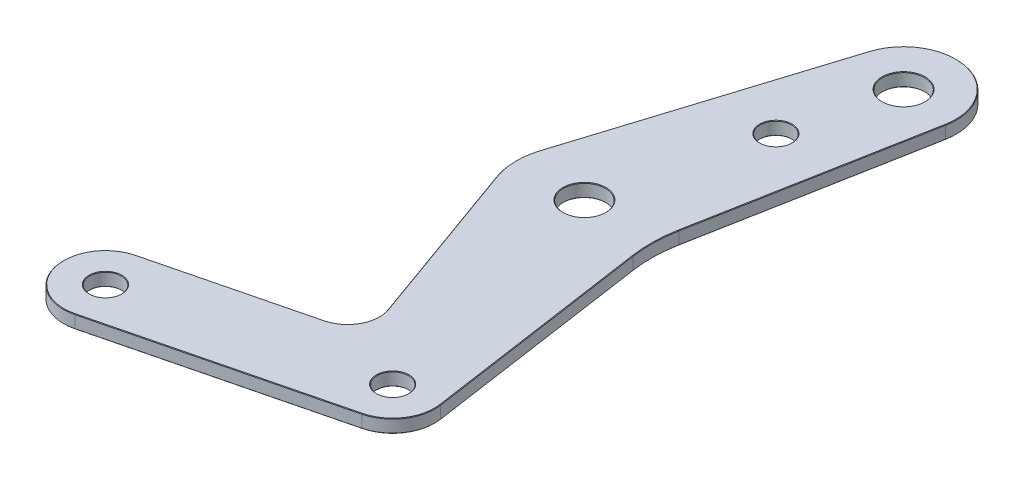
SolidWorks part; units mm, degrees
material "Plain Carbon Steel"
ref_plane "Front Plane" through (0, 0, 0) normal (0, 0, 1) x (1, 0, 0)
ref_plane "Top Plane" through (0, 0, 0) normal (0, 1, 0) x (1, 0, 0)
ref_plane "Right Plane" through (0, 0, 0) normal (1, 0, 0) x (0, 0, -1)
sketch "Sketch1" plane through (0, 0, 0) normal (0, 1, 0) x (1, 0, 0)
  line L0 (0, 0) -> (12.0961, 48.5148) construction
  line L1 (0, 0) -> (0, 50000) construction
  line L2 (0, 0) -> (50000, 0) construction
  line L3 (0, 0) -> (12.0961, -48.5148) construction
  line L4 (12.0961, -48.5148) -> (-31.5672, -59.4013) construction
  line L5 (-29.6318, -67.1636) -> (14.0315, -56.2772)
  line L6 (-33.5026, -51.6389) -> (-4.8571, -44.4968)
  line L7 (2.5558, 51.5118) -> (-12.4024, 3.8961)
  line L8 (-12.2361, -4.3906) -> (-0.6612, -36.6486)
  line L9 (13.7938, -4.5289) -> (20.0131, -47.3653)
  line L10 (21.9267, 46.6821) -> (13.9644, 3.9718)
  circle A0 centre (0, 0) radius 4
  circle A1 centre (12.0961, 48.5148) radius 4
  circle A2 centre (7.2577, 29.1089) radius 3
  circle A3 centre (12.0961, -48.5148) radius 3
  circle A4 centre (-31.5672, -59.4013) radius 3
  arc A5 (-33.5026, -51.6389) -> (-29.6318, -67.1636) centre (-31.5672, -59.4013) ccw
  arc A6 (14.0315, -56.2772) -> (20.0131, -47.3653) centre (12.0961, -48.5148) ccw
  arc A8 (21.9267, 46.6821) -> (2.5558, 51.5118) centre (12.0961, 48.5148) ccw
  arc A9 (-4.8571, -44.4968) -> (-0.6612, -36.6486) centre (-6.3086, -38.675) ccw
  arc A10 (-12.4024, 3.8961) -> (-12.2361, -4.3906) centre (0, 0) ccw
  arc A11 (13.7938, -4.5289) -> (13.9644, 3.9718) centre (39.5241, -0.7932) cw
  dimension "D1" = 8
  dimension "D4" = 8
  dimension "D5" = 6
  dimension "D9" = 6
  dimension "D11" = 6
  dimension "D12" = 16
  dimension "D13" = 16
  dimension "D14" = 26
  dimension "D15" = 20
  dimension "D16" = 6
  dimension "D2" = 50
  dimension "D3" = 14
  dimension "D6" = 20
  dimension "D7" = 50
  dimension "D8" = 14
  dimension "D10" = 45
  dimension "D17" = 5.739
  dimension "D18" = 3.44
  dimension "D19" = 5.739
  dimension "D20" = 3.44
extrude "Boss-Extrude1" add sketch "Sketch1" along normal mid plane 2.5
chamfer "Chamfer1" distance 0.1 angle 45 34 edges at (-31.5672, -1.25, 62.4013) (12.0961, -1.25, 51.5148) (7.2577, -1.25, -26.1089) (12.0961, -1.25, -44.5148) (0, -1.25, 4) (-19.1799, -1.25, 48.0678) (-39.3296, -1.25, 61.3366) (-7.8002, -1.25, 61.7204) (18.7386, -1.25, 52.9732) (16.9035, -1.25, 25.9471) (13.5293, -1.25, 0.2715) (17.9456, -1.25, -25.3269) (14.5153, -1.25, -58.2177) (-4.9233, -1.25, -27.704) (-12.9974, -1.25, 0.2608) (-6.4487, -1.25, 20.5196) (-1.0174, -1.25, 41.5039) (-31.5672, 1.25, 62.4013) (7.2577, 1.25, -26.1089) (0, 1.25, 4) (-6.4487, 1.25, 20.5196) (-12.9974, 1.25, 0.2608) (-4.9233, 1.25, -27.704) (14.5153, 1.25, -58.2177) (17.9456, 1.25, -25.3269) (13.5293, 1.25, 0.2715) (16.9035, 1.25, 25.9471) (18.7386, 1.25, 52.9732) (-7.8002, 1.25, 61.7204) (-39.3296, 1.25, 61.3366) (-19.1799, 1.25, 48.0678) (-1.0174, 1.25, 41.5039) (12.0961, 1.25, -44.5148) (12.0961, 1.25, 51.5148)
